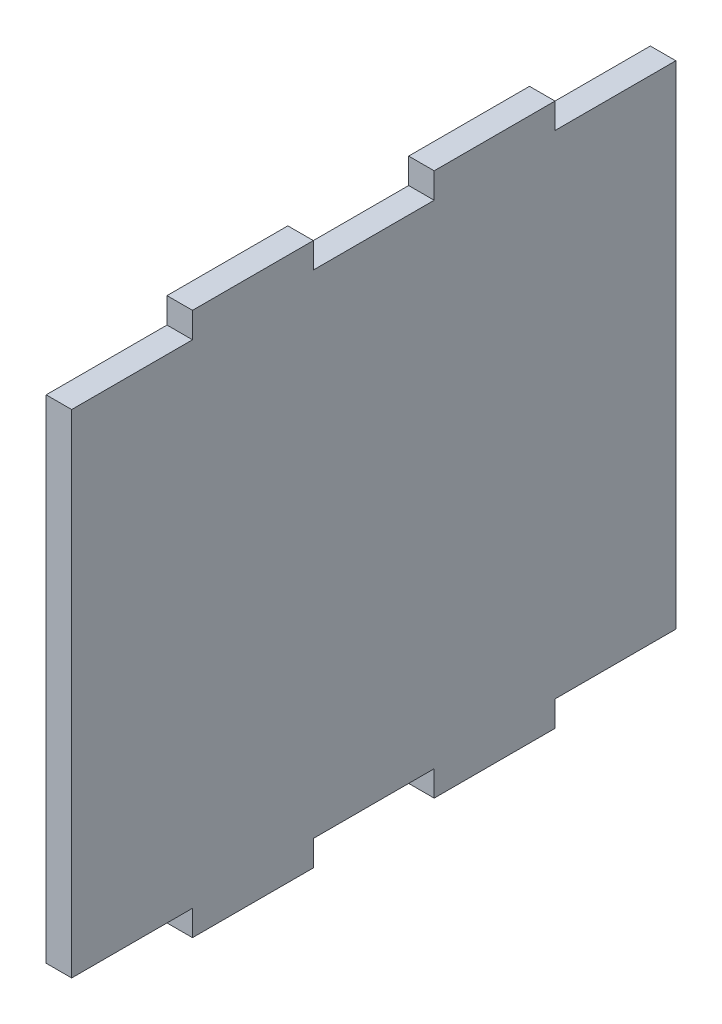
SolidWorks part; units mm, degrees
ref_plane "Front Plane" through (0, 0, 0) normal (0, 0, 1) x (1, 0, 0)
ref_plane "Top Plane" through (0, 0, 0) normal (0, 1, 0) x (1, 0, 0)
ref_plane "Right Plane" through (0, 0, 0) normal (1, 0, 0) x (0, 0, -1)
sketch "Sketch1" plane through (0, 0, 0) normal (1, 0, 0) x (0, 0, -1)
  line L1 (0, 0) -> (135, 0)
  line L2 (0, 0) -> (0, 122)
  line L3 (0, 122) -> (135, 122)
  line L4 (135, 0) -> (135, 122)
sketch "Sketch2" plane through (0, 0, 0) normal (1, 0, 0) x (0, 0, -1)
  line L0 (0, 116) -> (27, 116)
  line L2 (27, 116) -> (27, 121.7)
  line L4 (27, 121.7) -> (54, 121.7)
  line L5 (54, 121.7) -> (54, 116)
  line L6 (54, 116) -> (81, 116)
  line L7 (81, 116) -> (81, 121.7)
  line L8 (81, 121.7) -> (108, 121.7)
  line L9 (108, 121.7) -> (108, 116)
  line L10 (108, 116) -> (135, 116)
  line L12 (135, 116) -> (135, 130)
  line L13 (135, 130) -> (0, 130)
  line L14 (0, 130) -> (0, 116)
  line L16 (0, -8) -> (0, 6)
  line L17 (135, -8) -> (0, -8)
  line L18 (135, 6) -> (135, -8)
  line L19 (108, 6) -> (135, 6)
  line L20 (108, 0.3) -> (108, 6)
  line L21 (81, 0.3) -> (108, 0.3)
  line L22 (81, 6) -> (81, 0.3)
  line L23 (54, 6) -> (81, 6)
  line L24 (54, 0.3) -> (54, 6)
  line L25 (27, 0.3) -> (54, 0.3)
  line L26 (27, 6) -> (27, 0.3)
  line L27 (0, 6) -> (27, 6)
extrude "Boss-Extrude1" add sketch "Sketch1" along normal blind 5.7
extrude "Cut-Extrude1" cut sketch "Sketch2" along normal blind 57
